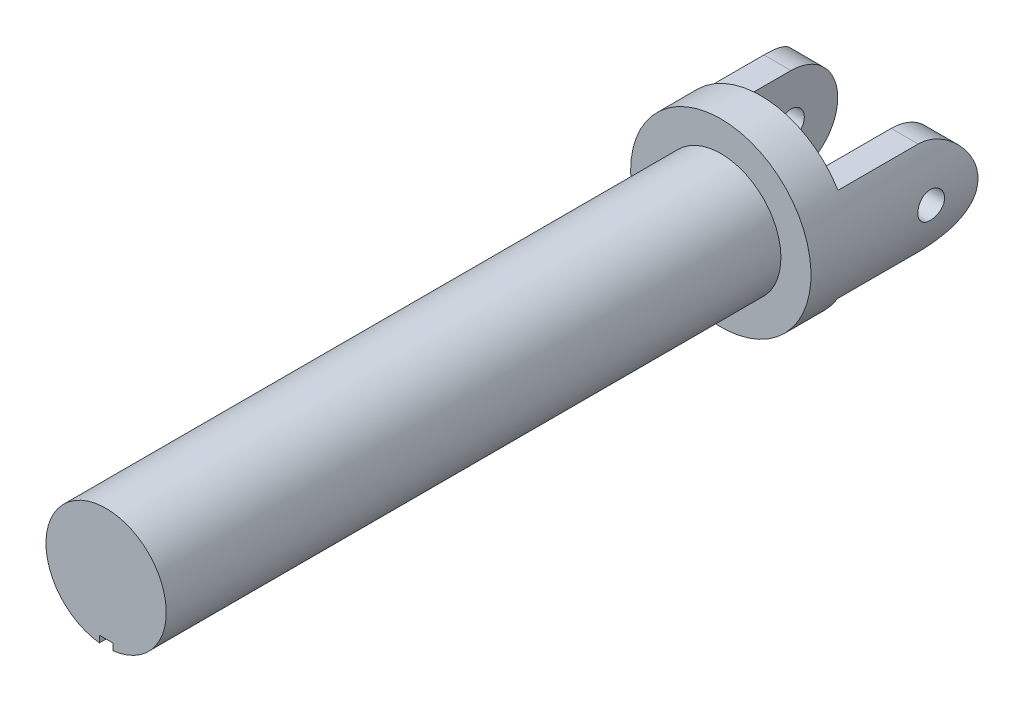
SolidWorks part; units mm, degrees
ref_plane "Front Plane" through (0, 0, 0) normal (0, 0, 1) x (1, 0, 0)
ref_plane "Top Plane" through (0, 0, 0) normal (0, 1, 0) x (1, 0, 0)
ref_plane "Right Plane" through (0, 0, 0) normal (1, 0, 0) x (0, 0, -1)
sketch "Sketch1" plane through (0, 0, 0) normal (0, 0, 1) x (1, 0, 0)
  circle A0 centre (0, 0) radius 4.5
  dimension "D1" = 9
extrude "Yoke" add sketch "Sketch1" along normal mid plane 46 contours A0
sketch "Sketch2" plane through (0, 0, -23) normal (0, 0, -1) x (-1, 0, 0)
  circle A0 centre (0, 0) radius 6.75
  dimension "D1" = 13.5
extrude "U Joint Base" add sketch "Sketch2" along normal blind 3
sketch "Sketch3" plane through (0, 0, -26) normal (0, 0, -1) x (-1, 0, 0)
  line L0 (-5.7717, 3.5) -> (-3.75, 3.5)
  line L1 (-3.75, 3.5) -> (-3.75, -3.5)
  line L2 (-3.75, -3.5) -> (-5.7717, -3.5)
  line L3 (3.75, -3.5) -> (3.75, 3.5)
  line L4 (3.75, 3.5) -> (5.7717, 3.5)
  line L5 (5.7717, -3.5) -> (3.75, -3.5)
  circle A0 centre (0, 0) radius 6.75 construction
  arc A1 (-5.7717, -3.5) -> (-5.7717, 3.5) centre (0, 0) cw
  arc A2 (5.7717, 3.5) -> (5.7717, -3.5) centre (0, 0) cw
  point P16 (0, 0)
  dimension "D2" = 7.5
  dimension "D3" = 7
  dimension "D1" = 2
extrude "U Joint Standups" add sketch "Sketch3" along normal blind 9.5
sketch "Sketch4" plane through (0, 0, 0) normal (1, 0, 0) x (0, 0, -1)
  line L0 (35.5, 3.5) -> (26, 3.5) construction
  line L1 (35.5, -3.5) -> (35.5, 3.5) construction
  line L2 (32, -3.5) -> (35.5, -3.5)
  line L3 (35.5, -3.5) -> (35.5, 0)
  line L4 (35.5, 0) -> (35.5, 3.5)
  line L5 (35.5, 3.5) -> (32, 3.5)
  line L6 (35.5, -3.5) -> (26, -3.5) construction
  arc A0 (35.5, 0) -> (32, 3.5) centre (32, 0) ccw
  arc A1 (32, -3.5) -> (35.5, 0) centre (32, 0) ccw
extrude "Standup Round" cut sketch "Sketch4" against normal through all both and the other way through all contours A1 L2 L3 | A0 L5 L4
sketch "Sketch5" plane through (0, 0, 0) normal (1, 0, 0) x (0, 0, -1)
  circle A0 centre (32, 0) radius 1
  dimension "D1" = 2
extrude "Ball Holes" cut sketch "Sketch5" against normal through all both and the other way through all
sketch "Sketch6" plane through (0, 0, 23) normal (0, 0, 1) x (1, 0, 0)
  line L0 (0.5, -4.4721) -> (0.5, -4.702)
  line L1 (-0.5, -4.4721) -> (-0.5, -3.9721)
  line L2 (-0.5, -3.9721) -> (0.5, -3.9721)
  line L3 (0.5, -3.9721) -> (0.5, -4.4721)
  line L4 (0.5, -4.702) -> (-0.5, -4.702)
  line L5 (-0.5, -4.702) -> (-0.5, -4.4721)
  circle A1 centre (0, 0) radius 4.5 construction
  circle A4 centre (0, 0) radius 4.5 construction
  dimension "D1" = 0.5
  dimension "D2" = 1
  dimension "D3" = 0.5
extrude "Keyway" cut sketch "Sketch6" against normal blind 46 contours L4 L5 L1 L2 L3 L0
